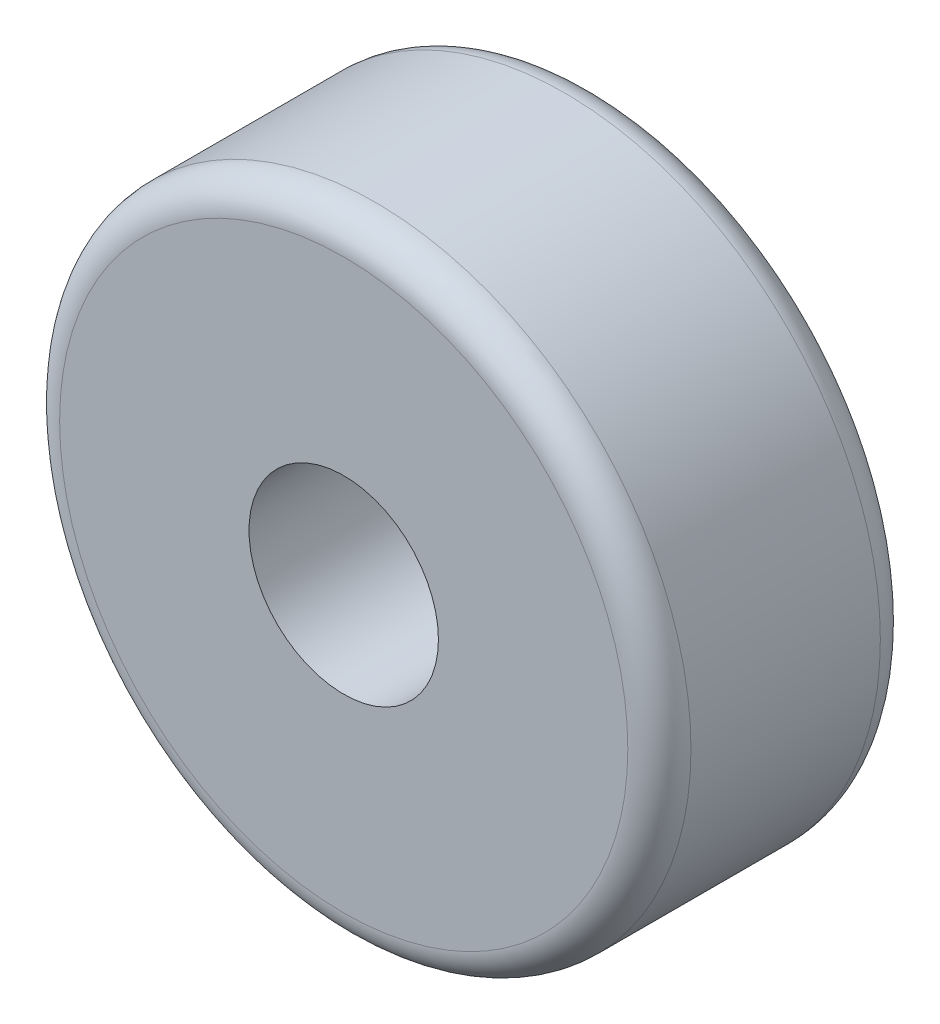
SolidWorks part; units mm, degrees
ref_plane "Plan de face" through (0, 0, 0) normal (0, 0, 1) x (1, 0, 0)
ref_plane "Plan de dessus" through (0, 0, 0) normal (0, 1, 0) x (1, 0, 0)
ref_plane "Plan de droite" through (0, 0, 0) normal (1, 0, 0) x (0, 0, -1)
sketch "Esquisse1" plane through (0, 0, 0) normal (0, 0, 1) x (1, 0, 0)
  circle A0 centre (0, 0) radius 1.5
  circle A1 centre (0, 0) radius 5
  dimension "D1" = 3
  dimension "D2" = 10
extrude "Boss.-Extru.1" add sketch "Esquisse1" along normal blind 4
fillet "Congé1" radius 0.5 2 edges at (5, 0, 0) (5, 0, 4)
